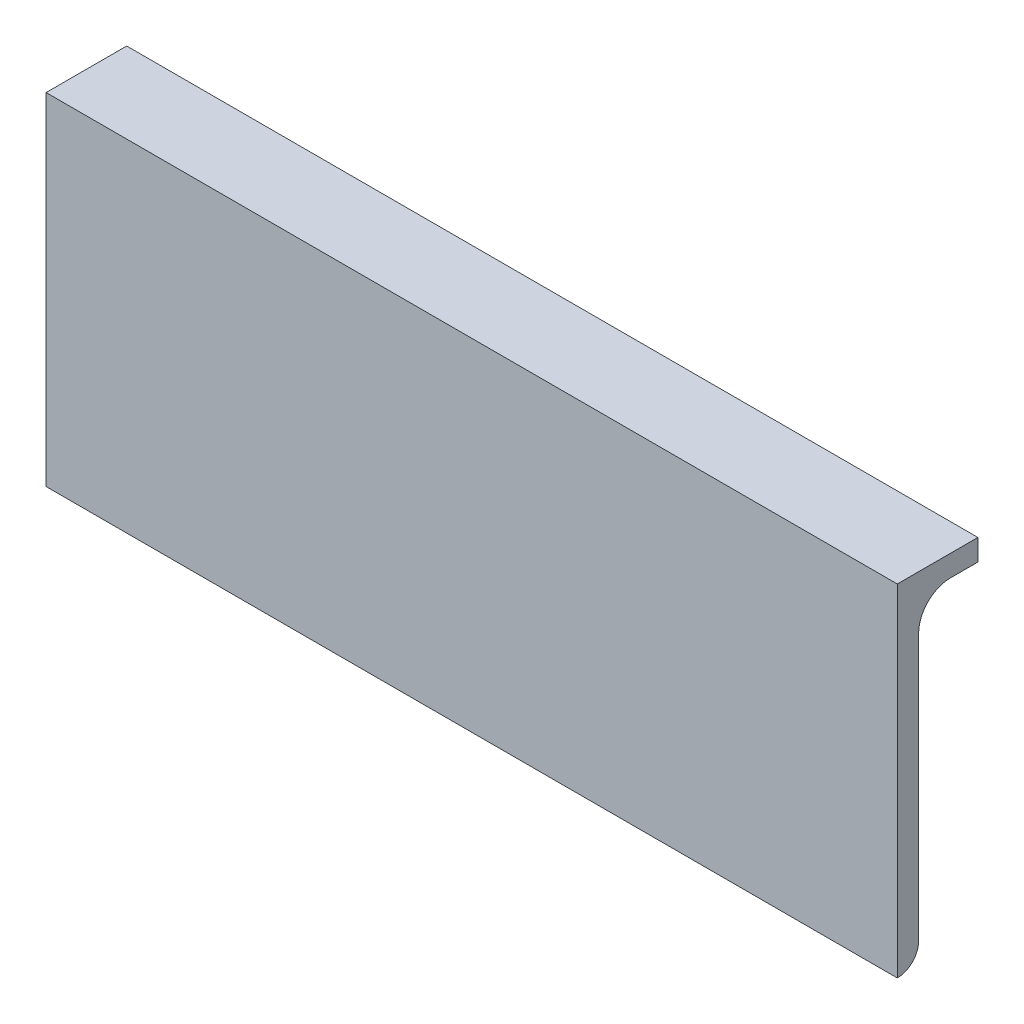
SolidWorks part; units mm, degrees
ref_plane "Alzado" through (0, 0, 0) normal (0, 0, 1) x (1, 0, 0)
ref_plane "Planta" through (0, 0, 0) normal (0, 1, 0) x (1, 0, 0)
ref_plane "Vista lateral" through (0, 0, 0) normal (1, 0, 0) x (0, 0, -1)
sketch "Croquis1" plane through (0, 0, 0) normal (0, 0, 1) x (1, 0, 0)
  line L0 (-63.36, 0) -> (63.36, 0)
  point P4 (0, 0)
  dimension "D1" = 126.72
other "Hierro angular 2 X 2 X 0.125(1)"
ref_plane "Plano1" through (-63.36, 0, 0) normal (1, 0, 0) x (0, -1, 0)
sketch "Sketch1" plane through (-63.36, 0, 0) normal (1, 0, 0) x (0, -1, 0)
  line L0 (0, 0) -> (0, 50.8)
  line L1 (0, 50.8) -> (0.0051, 50.8)
  line L2 (3.175, 47.6301) -> (3.175, 7.9375)
  line L3 (7.9375, 3.175) -> (47.6301, 3.175)
  line L4 (50.8, 0.0051) -> (50.8, 0)
  line L5 (50.8, 0) -> (0, 0)
  arc A0 (50.8, 0.0051) -> (47.6301, 3.175) centre (47.6301, 0.0051) ccw
  arc A1 (0.0051, 50.8) -> (3.175, 47.6301) centre (0.0051, 47.6301) cw
  arc A2 (7.9375, 3.175) -> (3.175, 7.9375) centre (7.9375, 7.9375) cw
  point P10 (25.4, 0)
  point P14 (0, 25.4)
  point P15 (3.175, 25.4)
  point P16 (25.4, 3.175)
  point P17 (3.175, 50.8)
  point P18 (50.8, 3.175)
  point P19 (0, 0)
  dimension "D2" = 0.0051
  dimension "Radius_1" = 4.7625
  dimension "D1" = 3.175
  dimension "H_leg" = 50.8
sketch "Croquis3" plane through (0, 0, 0) normal (0, 1, 0) x (1, 0, 0)
  line L0 (63.36, 12) -> (-63.36, 12)
  line L1 (63.36, 50.8) -> (63.36, 0) construction
  line L2 (-63.36, 50.8) -> (-63.36, 0) construction
  line L3 (-63.36, 0) -> (63.36, 0) construction
  line L4 (63.36, 12) -> (63.36, 50.8)
  line L5 (63.36, 50.8) -> (-63.36, 50.8)
  line L6 (-63.36, 50.8) -> (-63.36, 12)
  dimension "D1" = 12
extrude "Cortar-Extruir1" cut sketch "Croquis3" against normal up to surface (3.175 mm away) up to face at (0, -3.175, -27.7838)
